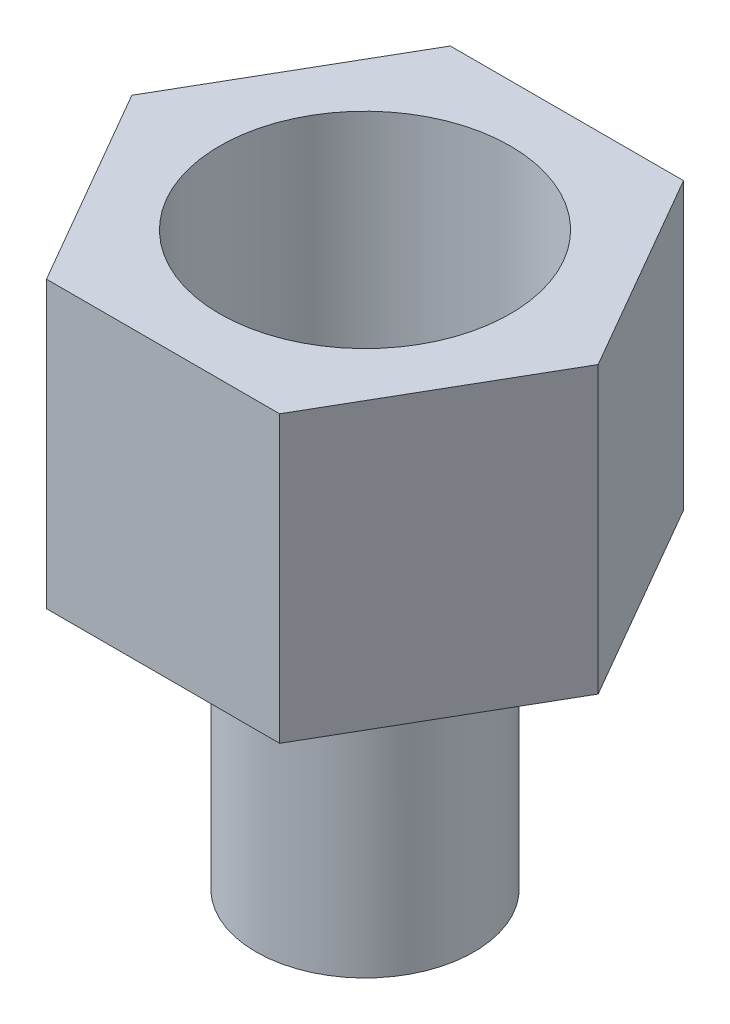
SolidWorks part; units mm, degrees
ref_plane "Front Plane" through (0, 0, 0) normal (0, 0, 1) x (1, 0, 0)
ref_plane "Top Plane" through (0, 0, 0) normal (0, 1, 0) x (1, 0, 0)
ref_plane "Right Plane" through (0, 0, 0) normal (1, 0, 0) x (0, 0, -1)
sketch "Sketch1" plane through (0, 0, 0) normal (0, 1, 0) x (1, 0, 0)
  line L0 (0, 0) -> (0, 9.525) construction
  line L1 (5.4993, 9.525) -> (-5.4993, 9.525)
  line L2 (-5.4993, 9.525) -> (-10.9985, 0)
  line L3 (-10.9985, 0) -> (-5.4993, -9.525)
  line L4 (-5.4993, -9.525) -> (5.4993, -9.525)
  line L5 (5.4993, -9.525) -> (10.9985, 0)
  line L6 (10.9985, 0) -> (5.4993, 9.525)
  circle A0 centre (0, 0) radius 9.525 construction
  dimension "D1" = 19.05
extrude "Boss-Extrude1" add sketch "Sketch1" against normal blind 13.462
sketch "Sketch2" plane through (0, 0, 0) normal (0, 1, 0) x (1, 0, 0)
  circle A0 centre (0, 0) radius 6.858
  dimension "D1" = 13.716
extrude "Cut-Extrude1" cut sketch "Sketch2" against normal offset from surface (12.954 mm away) 0.508 up to face at (0, -13.462, 0)
sketch "Sketch3" plane through (0, -13.462, 0) normal (0, -1, 0) x (1, 0, 0)
  circle A1 centre (0, 0) radius 5.1435
  dimension "D2" = 10.287
extrude "Boss-Extrude2" add sketch "Sketch3" along normal blind 13.462
sketch "Sketch4" plane through (0, -26.924, 0) normal (0, -1, 0) x (1, 0, 0)
  circle A0 centre (0, 0) radius 2.794
  dimension "D1" = 5.588
extrude "Cut-Extrude2" cut sketch "Sketch4" against normal through all
